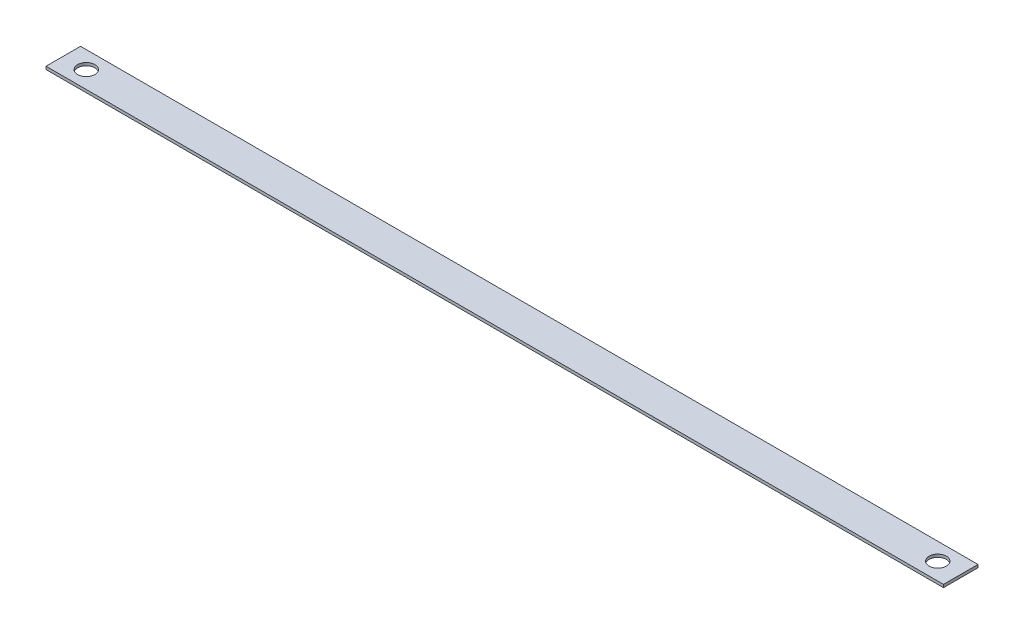
SolidWorks part; units mm, degrees
ref_plane "Front Plane" through (0, 0, 0) normal (0, 0, 1) x (1, 0, 0)
ref_plane "Top Plane" through (0, 0, 0) normal (0, 1, 0) x (1, 0, 0)
ref_plane "Right Plane" through (0, 0, 0) normal (1, 0, 0) x (0, 0, -1)
sketch "Sketch1" plane through (0, 0, 0) normal (0, 1, 0) x (1, 0, 0)
  line L0 (0, 0) -> (-469.9, 0) construction
  line L1 (495.3, -19.05) -> (-495.3, -19.05)
  line L2 (495.3, -19.05) -> (495.3, 19.05)
  line L3 (495.3, 19.05) -> (-495.3, 19.05)
  line L4 (-495.3, -19.05) -> (-495.3, 19.05)
  line L5 (495.3, -19.05) -> (-495.3, 19.05) construction
  line L6 (495.3, 19.05) -> (-495.3, -19.05) construction
  line L7 (0, 0) -> (0, -19.05) construction
  circle A0 centre (-469.9, 0) radius 9.525
  circle A1 centre (469.9, 0) radius 9.525
  point P0 (0, 0)
  dimension "D4" = 19.05
  dimension "D1" = 38.1
  dimension "D2" = 990.6
  dimension "D3" = 469.9
extrude "Boss-Extrude1" add sketch "Sketch1" along normal blind 3.175
